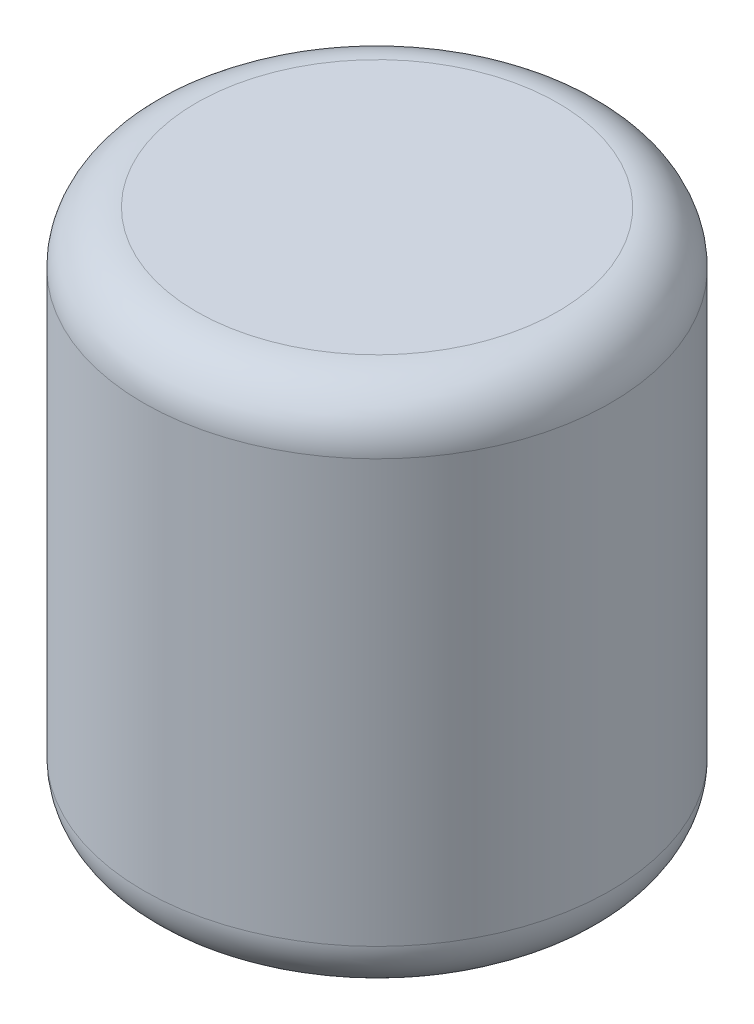
SolidWorks part; units mm, degrees
material "A-Glass Fiber"
ref_plane "Front" through (0, 0, 0) normal (0, 0, 1) x (1, 0, 0)
ref_plane "Top" through (0, 0, 0) normal (0, 1, 0) x (1, 0, 0)
ref_plane "Right" through (0, 0, 0) normal (1, 0, 0) x (0, 0, -1)
sketch "Sketch1" plane through (0, 0, 0) normal (0, 1, 0) x (1, 0, 0)
  circle A0 centre (0, 0) radius 44.25
  dimension "D1" = 88.5
extrude "Boss-Extrude1" add sketch "Sketch1" along normal blind 100
fillet "Fillet1" radius 10 2 edges at (0, 100, 44.25) (0, 0, 44.25)
